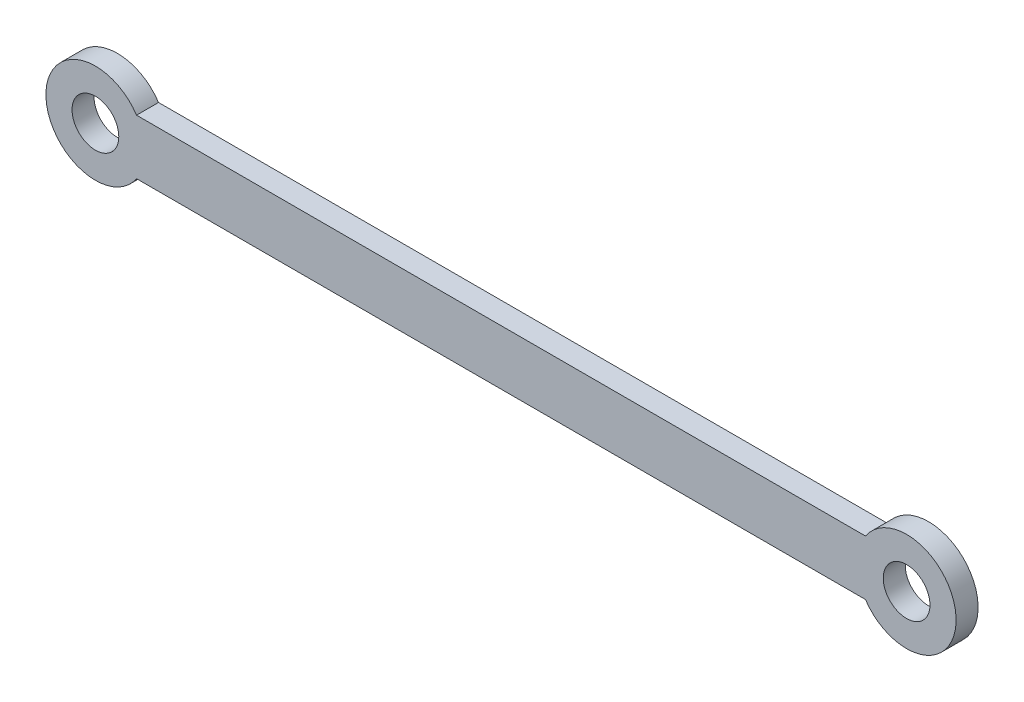
SolidWorks part; units mm, degrees
ref_plane "前视基准面" through (0, 0, 0) normal (0, 0, 1) x (1, 0, 0)
ref_plane "上视基准面" through (0, 0, 0) normal (0, 1, 0) x (1, 0, 0)
ref_plane "右视基准面" through (0, 0, 0) normal (1, 0, 0) x (0, 0, -1)
sketch "草图1" plane through (0, 0, 0) normal (0, 0, 1) x (1, 0, 0)
  line L0 (0, 0) -> (147.5, 0) construction
  line L1 (7.4833, 5) -> (140.0167, 5)
  line L2 (7.4833, -5) -> (140.0167, -5)
  arc A0 (7.4833, 5) -> (7.4833, -5) centre (0, 0) ccw
  arc A1 (140.0167, -5) -> (140.0167, 5) centre (147.5, 0) ccw
  circle A2 centre (0, 0) radius 4.25
  circle A3 centre (147.5, 0) radius 4.25
  dimension "D2" = 8.5
  dimension "D3" = 8.5
  dimension "D4" = 18
  dimension "D5" = 18
  dimension "D1" = 147.5
  dimension "D6" = 5
extrude "凸台-拉伸1" add sketch "草图1" along normal blind 4
